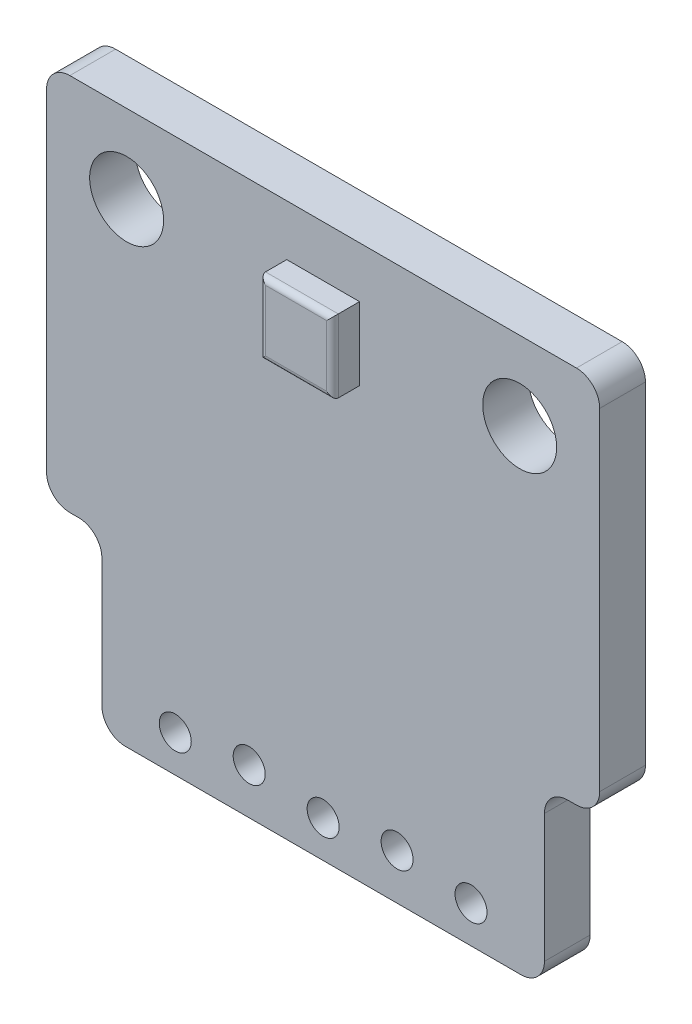
SolidWorks part; units mm, degrees
ref_plane "Front Plane" through (0, 0, 0) normal (0, 0, 1) x (1, 0, 0)
ref_plane "Top Plane" through (0, 0, 0) normal (0, 1, 0) x (1, 0, 0)
ref_plane "Right Plane" through (0, 0, 0) normal (1, 0, 0) x (0, 0, -1)
sketch "Sketch1" plane through (0, 0, 0) normal (0, 0, 1) x (1, 0, 0)
  line L0 (-9.5, 19) -> (-9.5, 6)
  line L1 (-9.5, 0) -> (9.5, 0) construction
  line L2 (-9.5, 0) -> (-9.5, 19) construction
  line L3 (-9.5, 19) -> (9.5, 19)
  line L4 (9.5, 0) -> (9.5, 19) construction
  line L5 (-9.5, 6) -> (-7.6, 6)
  line L6 (-7.6, 6) -> (-7.6, 0)
  line L7 (-7.6, 0) -> (7.6, 0)
  line L8 (7.6, 0) -> (7.6, 6)
  line L9 (7.6, 6) -> (9.5, 6)
  line L10 (9.5, 6) -> (9.5, 19)
  line L11 (-7.6, 6) -> (7.6, 6) construction
  line L12 (-6.75, 16.3) -> (6.75, 16.3) construction
  line L13 (0, 16.3) -> (0, 0) construction
  line L14 (0, 1.27) -> (2.54, 1.27) construction
  line L15 (2.54, 1.27) -> (5.08, 1.27) construction
  line L16 (0, 1.27) -> (-2.54, 1.27) construction
  line L17 (-2.54, 1.27) -> (-5.08, 1.27) construction
  line L18 (-2.54, 1.27) -> (-2.54, 1.57) construction
  line L19 (2.54, 1.27) -> (2.54, 1.57) construction
  line L20 (-2.54, 1.27) -> (-5.08, 1.27) construction
  circle A0 centre (-6.75, 16.3) radius 1.27
  circle A1 centre (6.75, 16.3) radius 1.27
  circle A2 centre (0, 1.27) radius 0.55
  circle A4 centre (-5.08, 1.27) radius 0.55
  circle A6 centre (5.08, 1.27) radius 0.55
  circle A7 centre (-2.54, 1.57) radius 0.55
  circle A8 centre (2.54, 1.57) radius 0.55
  point P4 (0, 0)
  point P23 (0, 1.27)
  dimension "D5" = 2.54
  dimension "D8" = 1.1
  dimension "D1" = 19
  dimension "D2" = 19
  dimension "D3" = 6
  dimension "D4" = 15.2
  dimension "D6" = 13.5
  dimension "D7" = 2.7
  dimension "D9" = 2.54
  dimension "D10" = 1.27
  dimension "D11" = 0.3
extrude "Boss-Extrude1" add sketch "Sketch1" along normal blind 1.57
fillet "Fillet1" radius 0.8 8 edges at (-7.6, 0, 0.785) (-7.6, 6, 0.785) (-9.5, 6, 0.785) (-9.5, 19, 0.785) (9.5, 19, 0.785) (9.5, 6, 0.785) (7.6, 6, 0.785) (7.6, 0, 0.785)
sketch "Sketch2" plane through (0, 0, 1.57) normal (0, 0, 1) x (1, 0, 0)
  line L0 (0, 16) -> (0, 0) construction
  line L1 (-1.25, 14.75) -> (1.25, 14.75)
  line L2 (-1.25, 14.75) -> (-1.25, 17.25)
  line L3 (-1.25, 17.25) -> (1.25, 17.25)
  line L4 (1.25, 14.75) -> (1.25, 17.25)
  line L5 (-1.25, 14.75) -> (1.25, 17.25) construction
  line L6 (-1.25, 17.25) -> (1.25, 14.75) construction
  line L7 (-6.8, 0) -> (6.8, 0) construction
  line L8 (8.7, 19) -> (-8.7, 19) construction
  point P0 (0, 16)
  dimension "D1" = 2.5
  dimension "D2" = 3
extrude "Boss-Extrude2" add sketch "Sketch2" along normal blind 0.93
fillet "Fillet2" radius 0.2 4 edges at (0, 14.75, 2.5) (-1.25, 16, 2.5) (0, 17.25, 2.5) (1.25, 16, 2.5)
